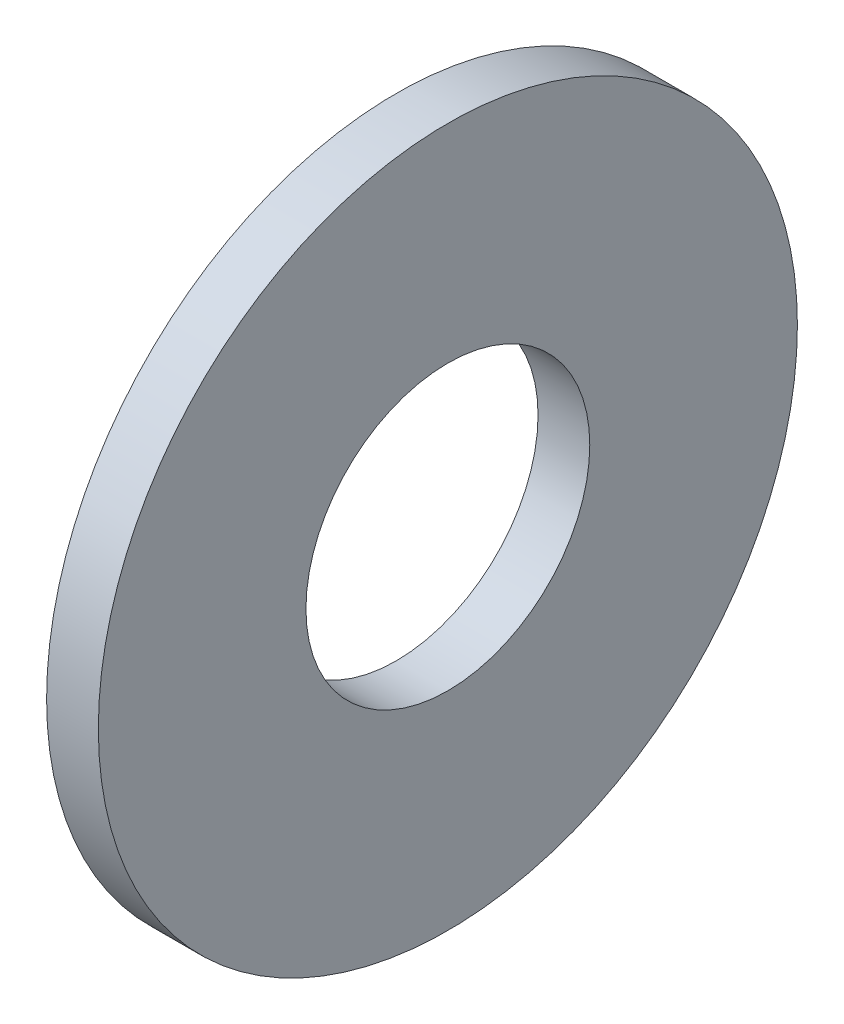
SolidWorks part; units mm, degrees
ref_plane "Front Plane" through (0, 0, 0) normal (0, 0, 1) x (1, 0, 0)
ref_plane "Top Plane" through (0, 0, 0) normal (0, 1, 0) x (1, 0, 0)
ref_plane "Right Plane" through (0, 0, 0) normal (1, 0, 0) x (0, 0, -1)
sketch "Sketch1" plane through (0, 0, 0) normal (1, 0, 0) x (0, 0, -1)
  circle A0 centre (0, 0) radius 12.7
  circle A1 centre (0, 0) radius 5.1562
  dimension "OD" = 25.4
  dimension "ID" = 10.3124
extrude "Boss-Extrude1" add sketch "Sketch1" along normal blind 1.8796
